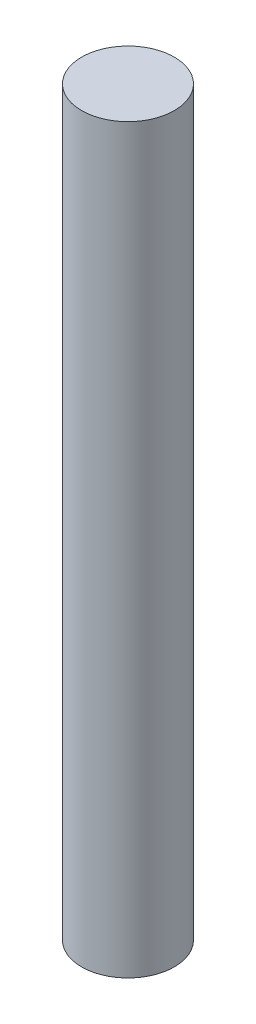
SolidWorks part; units mm, degrees
ref_plane "Front Plane" through (0, 0, 0) normal (0, 0, 1) x (1, 0, 0)
ref_plane "Top Plane" through (0, 0, 0) normal (0, 1, 0) x (1, 0, 0)
ref_plane "Right Plane" through (0, 0, 0) normal (1, 0, 0) x (0, 0, -1)
sketch "Sketch1" plane through (0, 0, 0) normal (0, 1, 0) x (1, 0, 0)
  circle A0 centre (0, 0) radius 3.175
  dimension "D1" = 6.35
extrude "Boss-Extrude1" add sketch "Sketch1" along normal blind 50.8 contours A0
equation "\"initial_heigh\"=2"
equation "\"initial_height\"=2"
